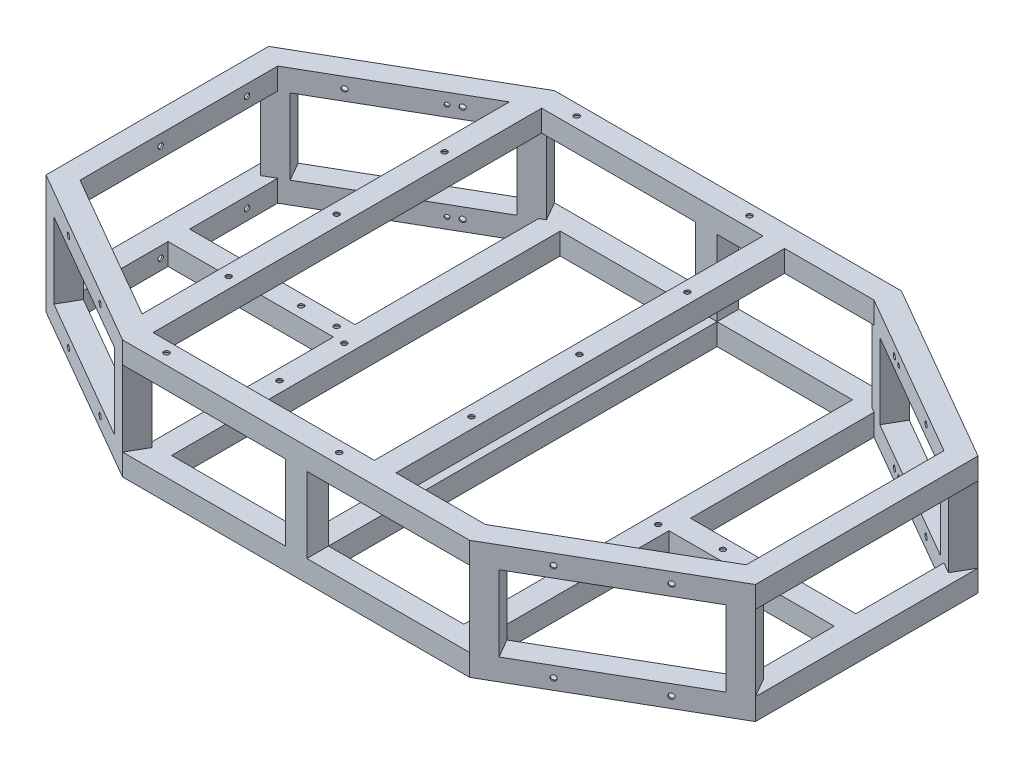
SolidWorks part; units mm, degrees
material "6061-T6 (SS)"
ref_plane "Front Plane" through (0, 0, 0) normal (0, 0, 1) x (1, 0, 0)
ref_plane "Top Plane" through (0, 0, 0) normal (0, 1, 0) x (1, 0, 0)
ref_plane "Right Plane" through (0, 0, 0) normal (1, 0, 0) x (0, 0, -1)
sketch "Sketch2" plane through (0, 0, 0) normal (1, 0, 0) x (0, 0, -1)
  line L0 (230.251, -11.049) -> (230.251, 11.049)
  line L5 (230.251, 11.049) -> (252.349, 11.049)
  line L6 (252.349, -11.049) -> (252.349, 11.049)
  line L7 (228.6, -12.7) -> (254, -12.7)
  line L8 (228.6, -12.7) -> (228.6, 12.7)
  line L9 (228.6, 12.7) -> (254, 12.7)
  line L10 (254, -12.7) -> (254, 12.7)
  line L11 (228.6, -12.7) -> (254, 12.7) construction
  line L12 (228.6, 12.7) -> (254, -12.7) construction
  line L13 (230.251, -11.049) -> (252.349, -11.049)
  point P5 (241.3, 0)
  dimension "D1" = 25.4
  dimension "D3" = 254
  dimension "D2" = 1.651
sketch "Sketch3" plane through (0, 0, 0) normal (0, 1, 0) x (1, 0, 0)
  line L0 (-190.5, 203.2) -> (190.5, 203.2)
  line L1 (0, 228.6) -> (0, 254) construction
  line L2 (0, 228.6) -> (0, 254) construction
  line L3 (190.5, 203.2) -> (366.4764, 101.6)
  line L4 (366.4764, 101.6) -> (366.4764, -101.6)
  line L5 (366.4764, -101.6) -> (190.5, -203.2)
  line L8 (190.5, -203.2) -> (-190.5, -203.2)
  line L9 (0, -203.2) -> (0, 203.2) construction
  line L10 (0, 0) -> (366.4764, 0) construction
  line L11 (-366.4764, -101.6) -> (-190.5, -203.2)
  line L12 (-366.4764, 101.6) -> (-366.4764, -101.6)
  line L13 (-190.5, 203.2) -> (-366.4764, 101.6)
  dimension "D1" = 381
  dimension "D2" = 30
  dimension "D3" = 203.2
  dimension "D4" = 203.2
  dimension "D5" = 203.2
  dimension "D6" = 30
sweep "Bottom Frame" add profiles "Sketch2" path "Sketch3"
sketch "Sketch4" plane through (0, 12.7, 0) normal (0, 1, 0) x (1, 0, 0)
  line L0 (-204.1118, -254) -> (-226.1089, -241.3)
  line L1 (-204.1118, -254) -> (-417.2764, -130.9294) construction
  line L2 (-226.1089, -241.3) -> (-213.4089, -219.303)
  line L3 (-197.3059, -228.6) -> (-391.8764, -116.2647) construction
  line L4 (-213.4089, -219.303) -> (-191.4118, -232.003)
  line L5 (-191.4118, -232.003) -> (-204.1118, -254)
  line L6 (-204.7161, -251.7447) -> (-223.8536, -240.6957)
  line L7 (-223.8536, -240.6957) -> (-212.8046, -221.5583)
  line L8 (-212.8046, -221.5583) -> (-193.6671, -232.6073)
  line L9 (-193.6671, -232.6073) -> (-204.7161, -251.7447)
  dimension "D2" = 1.651
  dimension "D1" = 25.4
extrude "Vertical Member 1" add sketch "Sketch4" along normal blind 88.9
sketch "Sketch5" plane through (0, 12.7, 0) normal (0, 1, 0) x (1, 0, 0)
  line L0 (-417.2764, -130.9294) -> (-395.2793, -143.6294)
  line L1 (-226.1089, -241.3) -> (-417.2764, -130.9294) construction
  line L2 (-395.2793, -143.6294) -> (-382.5793, -121.6323)
  line L3 (-213.4089, -219.303) -> (-391.8764, -116.2647) construction
  line L4 (-382.5793, -121.6323) -> (-404.5764, -108.9323)
  line L5 (-404.5764, -108.9323) -> (-417.2764, -130.9294)
  line L6 (-415.0211, -130.3251) -> (-395.8836, -141.3741)
  line L7 (-395.8836, -141.3741) -> (-384.8346, -122.2367)
  line L8 (-384.8346, -122.2367) -> (-403.9721, -111.1877)
  line L9 (-403.9721, -111.1877) -> (-415.0211, -130.3251)
  dimension "D2" = 1.651
  dimension "D1" = 25.4
extrude "Vertical Member 2" add sketch "Sketch5" along normal blind 88.9
mirror "Vertical Member 3 & 4" about plane through (0, 0, 0) normal (0, 0, 1) of "Vertical Member 1", "Vertical Member 2"
mirror "Vertical Members 5, 6, 7, 8" about plane through (0, 0, 0) normal (1, 0, 0) of "Vertical Member 3 & 4", "Vertical Member 1", "Vertical Member 2"
sketch "Sketch6" plane through (0, 12.7, 0) normal (0, 1, 0) x (1, 0, 0)
  line L0 (0, 0) -> (0, -254) construction
  line L1 (204.1118, -254) -> (-204.1118, -254) construction
  line L8 (197.3059, -228.6) -> (-197.3059, -228.6) construction
  line L9 (-12.7, -254) -> (12.7, -254)
  line L10 (-12.7, -254) -> (-12.7, -228.6)
  line L11 (-12.7, -228.6) -> (12.7, -228.6)
  line L12 (12.7, -254) -> (12.7, -228.6)
  line L13 (-11.049, -252.349) -> (-11.049, -230.251)
  line L14 (-11.049, -230.251) -> (11.049, -230.251)
  line L15 (11.049, -252.349) -> (11.049, -230.251)
  line L16 (-11.049, -252.349) -> (11.049, -252.349)
  point P11 (0, -254)
  dimension "D2" = 1.651
  dimension "D1" = 25.4
extrude "Middle Vertical Member 1" add sketch "Sketch6" along normal blind 88.9
mirror "Middle Vertical Member 2" about plane through (0, 0, 0) normal (0, 0, 1) of "Middle Vertical Member 1"
ref_plane "Top Frame Mirror Plane" through (0, 57.15, 0) normal (0, 1, 0) x (1, 0, 0)
mirror "Top Frame" about plane through (0, 57.15, 0) normal (0, 1, 0) of "Bottom Frame"
sketch "Sketch7" plane through (0, 0, 228.6) normal (0, 0, -1) x (-1, 0, 0)
  line L7 (12.7, 101.6) -> (12.7, 12.7) construction
  line L8 (-12.7, 12.7) -> (12.7, 12.7)
  line L9 (-12.7, 12.7) -> (-12.7, -12.7)
  line L10 (-12.7, -12.7) -> (12.7, -12.7)
  line L11 (12.7, 12.7) -> (12.7, -12.7)
  line L12 (-11.049, 11.049) -> (-11.049, -11.049)
  line L13 (-11.049, -11.049) -> (11.049, -11.049)
  line L14 (11.049, 11.049) -> (11.049, -11.049)
  line L15 (-11.049, 11.049) -> (11.049, 11.049)
  dimension "D2" = 1.651
  dimension "D1" = 25.4
extrude "Middle Support" add sketch "Sketch7" along normal up to surface (457.2 mm away) up to face at (0, 57.15, -228.6)
sketch "Sketch8" plane through (0, 0, 228.6) normal (0, 0, -1) x (-1, 0, 0)
  line L0 (12.7, -12.7) -> (197.3059, -12.7) construction
  line L1 (197.3059, 12.7) -> (171.9059, 12.7)
  line L2 (197.3059, 12.7) -> (197.3059, -12.7)
  line L3 (197.3059, -12.7) -> (171.9059, -12.7)
  line L4 (171.9059, 12.7) -> (171.9059, -12.7)
  line L5 (195.6549, 11.049) -> (195.6549, -11.049)
  line L6 (195.6549, -11.049) -> (173.5569, -11.049)
  line L7 (173.5569, 11.049) -> (173.5569, -11.049)
  line L8 (195.6549, 11.049) -> (173.5569, 11.049)
  dimension "D2" = 1.651
  dimension "D1" = 25.4
extrude "Bottom Support Rear" add sketch "Sketch8" along normal up to surface (457.2 mm away) up to face at (105.003, 0, -228.6)
sketch "Sketch9" plane through (-391.8764, 0, 0) normal (1, 0, 0) x (0, 0, -1)
  line L0 (-116.2647, 12.7) -> (116.2647, 12.7) construction
  line L1 (-12.7, 12.7) -> (12.7, 12.7)
  line L2 (-12.7, 12.7) -> (-12.7, -12.7)
  line L3 (-12.7, -12.7) -> (12.7, -12.7)
  line L4 (12.7, 12.7) -> (12.7, -12.7)
  line L5 (-116.2647, -12.7) -> (116.2647, -12.7) construction
  line L6 (-11.049, 11.049) -> (-11.049, -11.049)
  line L7 (-11.049, -11.049) -> (11.049, -11.049)
  line L8 (11.049, 11.049) -> (11.049, -11.049)
  line L9 (-11.049, 11.049) -> (11.049, 11.049)
  point P6 (0, -12.7)
  dimension "D2" = 1.651
  dimension "D1" = 25.4
extrude "I Beam" add sketch "Sketch9" along normal up to surface (194.5705 mm away) up to face at (-197.3059, 0, 0)
mirror "Bottom Support Front w/ I Beam" about plane through (0, 0, 0) normal (1, 0, 0) of "Bottom Support Rear", "I Beam"
sketch "Sketch10" plane through (0, 0, 228.6) normal (0, 0, -1) x (-1, 0, 0)
  line L0 (195.326, 103.251) -> (195.326, 125.349)
  line L1 (193.675, 101.6) -> (219.075, 101.6)
  line L2 (193.675, 101.6) -> (193.675, 127)
  line L3 (193.675, 127) -> (219.075, 127)
  line L4 (219.075, 101.6) -> (219.075, 127)
  line L5 (193.675, 101.6) -> (219.075, 127) construction
  line L6 (193.675, 127) -> (219.075, 101.6) construction
  line L7 (195.326, 125.349) -> (217.424, 125.349)
  line L8 (217.424, 103.251) -> (217.424, 125.349)
  line L9 (195.326, 103.251) -> (217.424, 103.251)
  line L10 (197.3059, 127) -> (-197.3059, 127) construction
  line L11 (197.3059, 101.6) -> (12.7, 101.6) construction
  point P0 (206.375, 114.3)
  dimension "D2" = 1.651
  dimension "D1" = 25.4
  dimension "D3" = 206.375
extrude "Top Rear Support" add sketch "Sketch10" along normal up to surface (457.2 mm away) up to face at (92.303, 0, -228.6)
ref_plane "Top Support Plane" through (-63.5, 0, 0) normal (1, 0, 0) x (0, 0, -1)
mirror "Top Front Support" about plane through (-63.5, 0, 0) normal (1, 0, 0) of "Top Rear Support"
sketch "Top Rear Support Holes" plane through (0, 127, 0) normal (0, 1, 0) x (1, 0, 0)
  line L0 (-206.375, 127) -> (-206.375, -127) construction
  line L1 (-219.075, 216.0316) -> (-219.075, -216.0316) construction
  point P4 (-206.375, 0)
  point P5 (-219.075, 0)
  dimension "D1" = 254
  dimension "D2" = 12.7
hole_wizard "1/4 (0.25) Diameter Hole 1" positions "Sketch12" profile "Sketch13" hole size "1/4" standard "ANSI Inch" end condition through all
sketch "Sketch12" plane through (0, 127, 0) normal (0, 1, 0) x (1, 0, 0)
  point P0 (-206.375, 127)
  point P3 (-206.375, -127)
  point P6 (-206.375, 0)
sketch "Sketch13" plane through (-206.375, 127, -127) normal (1, 0, 0) x (0, 0, 1)
  line L0 (0, 0) -> (0, 139.7)
  line L1 (0, 139.7) -> (3.175, 139.7)
  line L2 (3.175, 139.7) -> (3.175, 0)
  line L5 (3.175, 0) -> (0, 0)
  line L11 (0, -6.35) -> (0, 107.95) construction
  dimension "Thru Hole Dia." = 6.35
  dimension "Thru Hole Depth" = 139.7
mirror "1/4 (0.25) Diameter Hole 2" about plane through (-63.5, 0, 0) normal (1, 0, 0) of "1/4 (0.25) Diameter Hole 1"
sketch "Right SIde Holes" plane through (0, 127, 0) normal (0, 1, 0) x (1, 0, 0)
  line L0 (-165.1, -241.3) -> (38.1, -241.3) construction
  line L1 (-193.675, -228.6) -> (66.675, -228.6) construction
  point P2 (-63.5, -241.3)
  dimension "D1" = 203.2
  dimension "D2" = 63.5
  dimension "D3" = 12.7
hole_wizard "1/4 (0.25) Diameter Hole 3" positions "Sketch15" profile "Sketch17" hole size "1/4" standard "ANSI Inch"
sketch "Sketch15" plane through (0, 127, 0) normal (0, 1, 0) x (1, 0, 0)
  point P0 (-165.1, -241.3)
  point P3 (38.1, -241.3)
sketch "Sketch17" plane through (-165.1, 127, 241.3) normal (1, 0, 0) x (0, 0, 1)
  line L0 (0, 0) -> (0, 52.7077)
  line L1 (0, 52.7077) -> (3.175, 50.8)
  line L2 (3.175, 50.8) -> (3.175, 0)
  line L5 (3.175, 0) -> (0, 0)
  line L10 (0, 52.7077) -> (-3.175, 50.8) construction
  line L11 (0, -6.35) -> (0, 107.95) construction
  dimension "Hole Dia." = 6.35
  dimension "Hole Depth" = 50.8
  dimension "Drill Angle" = 118
mirror "1/4 (0.25) Diameter Hole 4" about plane through (0, 0, 0) normal (0, 0, 1) of "1/4 (0.25) Diameter Hole 3"
sketch "Hole Location" plane through (-161.0132, 0, 278.883) normal (-0.5, 0, 0.866) x (0.866, 0, 0.5)
  line L0 (-223.6366, 114.3) -> (-122.0366, 114.3) construction
  line L1 (-270.5072, 101.6) -> (-75.166, 101.6) construction
  point P4 (-172.8366, 114.3)
  point P5 (-172.8366, 101.6)
  dimension "D1" = 101.6
  dimension "D2" = 12.7
hole_wizard "1/4 (0.25) Diameter Hole3" positions "Sketch19" profile "Sketch20" hole size "1/4" standard "ANSI Inch"
sketch "Sketch19" plane through (-161.0132, 0, 278.883) normal (-0.5, 0, 0.866) x (0.866, 0, 0.5)
  point P0 (-223.6366, 114.3)
  point P3 (-122.0366, 114.3)
sketch "Sketch20" plane through (-354.6882, 114.3, 167.0647) normal (0, 1, 0) x (0.866, 0, 0.5)
  line L0 (0, 0) -> (0, 52.7077)
  line L1 (0, 52.7077) -> (3.175, 50.8)
  line L2 (3.175, 50.8) -> (3.175, 0)
  line L5 (3.175, 0) -> (0, 0)
  line L10 (0, 52.7077) -> (-3.175, 50.8) construction
  line L11 (0, -6.35) -> (0, 107.95) construction
  dimension "Hole Dia." = 6.35
  dimension "Hole Depth" = 50.8
  dimension "Drill Angle" = 118
mirror "Hole Location 1" about plane through (0, 57.15, 0) normal (0, 1, 0) of "1/4 (0.25) Diameter Hole3"
mirror "Hole Location 2" about plane through (0, 0, 0) normal (0, 0, 1) of "Hole Location 1", "1/4 (0.25) Diameter Hole3"
mirror "Hole Location 3" about plane through (0, 0, 0) normal (1, 0, 0) of "Hole Location 2", "1/4 (0.25) Diameter Hole3", "Hole Location 1"
sketch "Sketch22" plane through (-148.3132, 0, -256.886) normal (0.5, 0, 0.866) x (0.866, 0, -0.5)
  line L0 (-135.491, 114.3) -> (10.559, 114.3) construction
  line L2 (-62.466, 101.6) -> (-62.466, 127) construction
  line L3 (-75.166, 101.6) -> (-49.766, 101.6) construction
  line L4 (-81.7087, 127) -> (-281.2425, 127) construction
  circle A0 centre (-135.491, 114.3) radius 2.54
  circle A1 centre (10.559, 114.3) radius 2.54
  point P9 (-62.466, 114.3)
  dimension "D2" = 5.08
  dimension "D3" = 5.08
  dimension "D1" = 146.05
extrude "Inner Hole Location 1" cut sketch "Sketch22" against normal blind 6.35
mirror "Inner Hole Location 2" about plane through (0, 57.15, 0) normal (0, 1, 0) of "Inner Hole Location 1"
mirror "Inner Hole Location 3" about plane through (0, 0, 0) normal (0, 0, 1) of "Inner Hole Location 2", "Inner Hole Location 1"
mirror "Inner Hole Location 4" about plane through (0, 0, 0) normal (1, 0, 0) of "Inner Hole Location 3", "Inner Hole Location 1", "Inner Hole Location 2"
sketch "Sketch23" plane through (0, 12.7, 0) normal (0, 1, 0) x (1, 0, 0)
  line L1 (-197.3059, 12.7) -> (-391.8764, 12.7) construction
  line L2 (-197.3059, 228.6) -> (-197.3059, 12.7) construction
  line L3 (-219.075, -228.6) -> (-197.3059, -228.6) construction
  line L4 (-197.3059, -12.7) -> (-197.3059, -228.6) construction
  circle A0 centre (-248.1059, 0) radius 3.175
  circle A1 centre (-184.6059, -88.9) radius 3.175
  circle A2 centre (-184.6059, -12.7) radius 3.175
  dimension "D1" = 6.35
  dimension "D2" = 12.7
  dimension "D3" = 50.8
  dimension "D4" = 139.7
  dimension "D5" = 215.9
  dimension "D6" = 12.7
  dimension "D7" = 12.7
extrude "Rear Shock Mount Holes" cut sketch "Sketch23" against normal through all
mirror "Front Shock Mount Holes" about plane through (0, 0, 0) normal (1, 0, 0) of "Rear Shock Mount Holes"
sketch "Sketch24" plane through (0, 101.6, 0) normal (0, -1, 0) x (1, 0, 0)
  line L0 (-206.375, 130.175) -> (-206.375, 123.825) construction
  line L1 (-193.675, 228.6) -> (-12.7, 228.6) construction
  line L2 (-206.375, 3.175) -> (-206.375, -3.175) construction
  line L3 (-12.7, -228.6) -> (-193.675, -228.6) construction
  line L4 (-206.375, -123.825) -> (-206.375, -130.175) construction
  line L5 (66.675, 0) -> (-193.675, 0) construction
  line L6 (66.675, -228.6) -> (66.675, 228.6) construction
  line L7 (-193.675, -228.6) -> (-193.675, 228.6) construction
  line L8 (-63.5, 0) -> (-63.5, 228.6) construction
  circle A0 centre (-206.375, 190.5) radius 1.2446
  circle A1 centre (-206.375, 165.1) radius 1.2446
  circle A2 centre (-206.375, 127) radius 3.175 construction
  circle A3 centre (-206.375, 63.5) radius 1.2446
  circle A4 centre (-206.375, 38.1) radius 1.2446
  circle A5 centre (-206.375, 0) radius 3.175 construction
  circle A6 centre (-206.375, -165.1) radius 1.2446
  circle A7 centre (-206.375, -190.5) radius 1.2446
  circle A8 centre (-206.375, -127) radius 3.175 construction
  circle A9 centre (79.375, 190.5) radius 1.2446
  circle A10 centre (79.375, 165.1) radius 1.2446
  circle A11 centre (79.375, 63.5) radius 1.2446
  circle A12 centre (79.375, 38.1) radius 1.2446
  circle A13 centre (79.375, -165.1) radius 1.2446
  circle A14 centre (79.375, -190.5) radius 1.2446
  dimension "D1" = 2.4892
  dimension "D2" = 38.1
  dimension "D3" = 25.4
  dimension "D4" = 101.6
  dimension "D5" = 25.4
  dimension "D6" = 38.1
  dimension "D7" = 25.4
extrude "Z Direction Holes" cut sketch "Sketch24" against normal blind 1.651
sketch "Sketch25" plane through (0, 101.6, 0) normal (0, -1, 0) x (1, 0, 0)
  line L0 (-168.275, -241.3) -> (-161.925, -241.3) construction
  line L1 (66.675, 0) -> (-193.675, 0) construction
  line L2 (66.675, -228.6) -> (66.675, 228.6) construction
  line L3 (-193.675, -228.6) -> (-193.675, 228.6) construction
  line L4 (-63.5, 0) -> (-63.5, -228.6) construction
  line L5 (-12.7, -228.6) -> (-193.675, -228.6) construction
  circle A0 centre (75.2882, -241.3) radius 1.2446
  circle A1 centre (49.8882, -241.3) radius 1.2446
  circle A2 centre (-165.1, -241.3) radius 3.175 construction
  circle A3 centre (-176.8882, -241.3) radius 1.2446
  circle A4 centre (-202.2882, -241.3) radius 1.2446
  circle A5 centre (-176.8882, 241.3) radius 1.2446
  circle A6 centre (-202.2882, 241.3) radius 1.2446
  circle A7 centre (49.8882, 241.3) radius 1.2446
  circle A8 centre (75.2882, 241.3) radius 1.2446
  dimension "D1" = 2.4892
  dimension "D2" = 254
  dimension "D3" = 25.4
extrude "X Direction Holes" cut sketch "Sketch25" against normal blind 1.651
sketch "Sketch26" plane through (-417.2764, 0, 0) normal (-1, 0, 0) x (0, 0, 1)
  line L0 (-130.9294, 101.6) -> (-130.9294, 127) construction
  line L1 (-130.9294, 127) -> (130.9294, 127) construction
  line L2 (-130.9294, 57.15) -> (130.9294, 57.15) construction
  line L3 (-130.9294, 101.6) -> (-130.9294, 12.7) construction
  line L4 (130.9294, 101.6) -> (130.9294, 12.7) construction
  circle A0 centre (-80.1294, 114.3) radius 3.175
  circle A1 centre (21.4706, 114.3) radius 3.175
  circle A4 centre (21.4706, 0) radius 3.175
  circle A5 centre (-80.1294, 0) radius 3.175
  dimension "D1" = 6.35
  dimension "D2" = 50.8
  dimension "D3" = 101.6
  dimension "D4" = 12.7
extrude "Rear Holes" cut sketch "Sketch26" against normal blind 25.4
sketch "Sketch27" plane through (0, -12.7, 0) normal (0, -1, 0) x (1, 0, 0)
  line L1 (-171.9059, -228.6) -> (-171.9059, -254) construction
  line L4 (-204.1118, -254) -> (204.1118, -254) construction
  line L5 (-391.8764, -116.2647) -> (-417.2764, -116.2647) construction
  line L6 (-417.2764, 130.9294) -> (-417.2764, -130.9294) construction
  line L7 (391.8764, -116.2647) -> (417.2764, -116.2647) construction
  line L8 (417.2764, -130.9294) -> (417.2764, 130.9294) construction
  line L9 (-417.2764, 0) -> (417.2764, 0) construction
  circle A0 centre (-184.5538, -241.3) radius 1.2446
  circle A1 centre (-66.1898, -241.3) radius 1.2446
  circle A2 centre (55.2222, -241.3) radius 1.2446
  circle A3 centre (176.8882, -241.3) radius 1.2446
  circle A4 centre (298.5542, -241.3) radius 1.2446
  circle A5 centre (419.9662, -241.3) radius 1.2446
  circle A6 centre (184.5538, -241.3) radius 1.2446
  circle A7 centre (-404.5764, -123.5634) radius 1.2446
  circle A8 centre (404.5764, -123.5634) radius 1.2446
  circle A9 centre (404.5764, 123.5634) radius 1.2446
  circle A10 centre (184.5538, 241.3) radius 1.2446
  circle A11 centre (419.9662, 241.3) radius 1.2446
  circle A12 centre (298.5542, 241.3) radius 1.2446
  circle A13 centre (176.8882, 241.3) radius 1.2446
  circle A14 centre (55.2222, 241.3) radius 1.2446
  circle A15 centre (-66.1898, 241.3) radius 1.2446
  circle A16 centre (-184.5538, 241.3) radius 1.2446
  circle A17 centre (-404.5764, 123.5634) radius 1.2446
  point P20 (-171.9059, -241.3)
  point P29 (-404.5764, -116.2647)
  point P38 (404.5764, -116.2647)
  dimension "D1" = 2.4892
  dimension "D2" = 19.558
  dimension "D3" = 137.922
  dimension "D4" = 259.334
  dimension "D5" = 381
  dimension "D6" = 502.666
  dimension "D7" = 624.078
  dimension "D8" = 19.558
  dimension "D9" = 7.366
  dimension "D10" = 7.366
extrude "Cut-Extrude5" cut sketch "Sketch27" against normal blind 1.651
equation "\"Tubing\"= 1in"
equation "\"Wall Thickness\"= 0.065"
equation "\"D1@Sketch2\" = \"Tubing\""
equation "\"D2@Sketch2\"= \"Wall Thickness\""
equation "\"D1@Sketch4\"= \"Tubing\""
equation "\"D2@Sketch4\"= \"Wall Thickness\""
equation "\"D1@Sketch5\"= \"Tubing\""
equation "\"D2@Sketch5\"= \"Wall Thickness\""
equation "\"D1@Sketch6\"= \"Tubing\""
equation "\"D2@Sketch6\"= \"Wall Thickness\""
equation "\"D1@Sketch7\"= \"Tubing\""
equation "\"D2@Sketch7\"= \"Wall Thickness\""
equation "\"D1@Sketch8\"= \"Tubing\""
equation "\"D2@Sketch8\"= \"Wall Thickness\""
equation "\"D1@Sketch9\"= \"Tubing\""
equation "\"D2@Sketch9\"= \"Wall Thickness\""
equation "\"D1@Sketch10\"= \"Tubing\""
equation "\"D2@Sketch10\"= \"Wall Thickness\""
